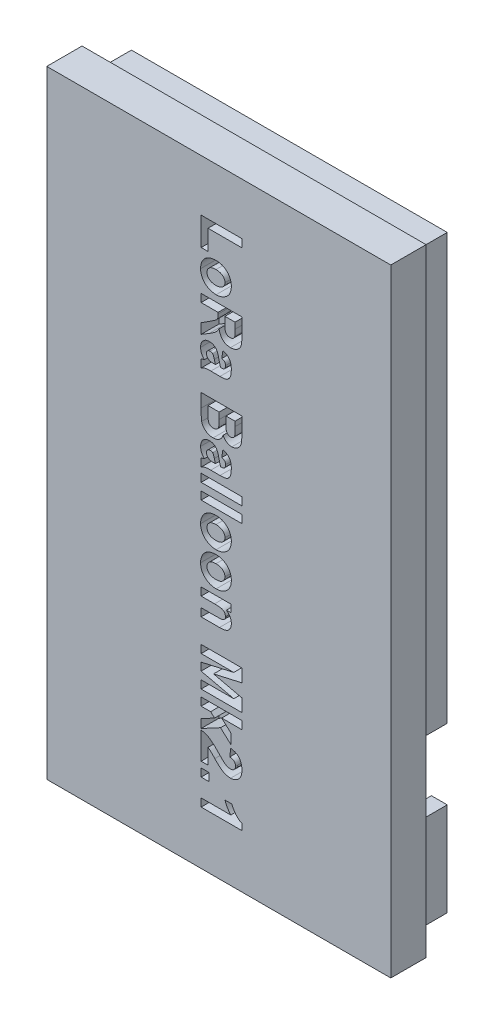
SolidWorks part; units mm, degrees
ref_plane "Front Plane" through (0, 0, 0) normal (0, 0, 1) x (1, 0, 0)
ref_plane "Top Plane" through (0, 0, 0) normal (0, 1, 0) x (1, 0, 0)
ref_plane "Right Plane" through (0, 0, 0) normal (1, 0, 0) x (0, 0, -1)
sketch "Sketch1" plane through (0, 0, 0) normal (0, 0, 1) x (1, 0, 0)
  line L1 (0, 0) -> (39, 0)
  line L2 (0, 0) -> (0, 70)
  line L3 (0, 70) -> (39, 70)
  line L4 (39, 0) -> (39, 70)
  dimension "D1" = 70
  dimension "D2" = 39
extrude "Base" add sketch "Sketch1" along normal blind 4
sketch "Sketch2" plane through (0, 0, 0) normal (0, 0, -1) x (-1, 0, 0)
  line L0 (-39, 0) -> (-39, 70) construction
  line L1 (-37.4, 68.4) -> (-35.6, 68.4)
  line L2 (-37.4, 68.4) -> (-37.4, 1.6)
  line L3 (-37.4, 1.6) -> (-35.6, 1.6)
  line L4 (-35.6, 68.4) -> (-35.6, 1.6)
  line L5 (0, 0) -> (-39, 0) construction
  line L6 (0, 70) -> (0, 0) construction
  line L7 (-35.6, 1.6) -> (-1.6, 1.6)
  line L8 (-35.6, 1.6) -> (-35.6, 3.4)
  line L9 (-35.6, 3.4) -> (-1.6, 3.4)
  line L10 (-1.6, 1.6) -> (-1.6, 3.4)
  line L12 (-39, 70) -> (0, 70) construction
  line L13 (-39, 35) -> (0, 35) construction
  line L14 (-19.5, 70) -> (-19.5, 0) construction
  line L15 (-35.6, 66.6) -> (-1.6, 66.6)
  line L16 (-1.6, 68.4) -> (-1.6, 66.6)
  line L17 (-35.6, 68.4) -> (-1.6, 68.4)
  line L18 (-35.6, 68.4) -> (-35.6, 66.6)
  line L19 (-1.6, 1.6) -> (-3.4, 1.6)
  line L20 (-3.4, 68.4) -> (-3.4, 1.6)
  line L21 (-1.6, 68.4) -> (-3.4, 68.4)
  line L22 (-1.6, 68.4) -> (-1.6, 1.6)
  dimension "D1" = 1.6
  dimension "D2" = 1.8
  dimension "D3" = 1.6
  dimension "D4" = 1.8
extrude "Mount" add sketch "Sketch2" along normal blind 4 contours L4 L1 L2 L3 | L22 L15 L20 L9 | L20 L9 L4 L7 | L9 L20 L7 L10 | L17 L20 L15 L16 | L20 L17 L4 L15
sketch "Sketch3" plane through (0, 0, 4) normal (0, 0, 1) x (1, 0, 0)
  line L0 (17.5, 0) -> (17.5, 70) construction
  line L1 (19.5, 0) -> (19.5, 5) construction
  line L2 (19.5, 70) -> (19.5, 65) construction
  line L3 (39, 70) -> (0, 70) construction
  line L4 (0, 0) -> (39, 0) construction
  line L6 (0, 70) -> (0, 0) construction
  text T0 "<b>  LoRa Balloon Mk2.1</b>" font "Arial Narrow" height in points 18
  dimension "D1" = 17.5
  dimension "D2" = 70
  dimension "D3" = 5
  dimension "D4" = 5
extrude "Name" cut sketch "Sketch3" against normal blind 2
sketch "Sketch4" plane through (35.6, 0, 0) normal (-1, 0, 0) x (0, 0, 1)
  line L0 (-4, 66.6) -> (-4, 3.4) construction
  line L1 (-4, 12.2) -> (0, 12.2)
  line L2 (-4, 12.2) -> (-4, 20.2)
  line L3 (-4, 20.2) -> (0, 20.2)
  line L4 (0, 12.2) -> (0, 20.2)
  line L5 (0, 66.6) -> (0, 3.4) construction
  line L6 (-4, 3.4) -> (0, 3.4) construction
  dimension "D1" = 8.8
  dimension "D2" = 8
extrude "Cut-Extrude1" cut sketch "Sketch4" against normal blind 1.8
sketch "Sketch5" plane through (0, 1.6, 0) normal (0, -1, 0) x (1, 0, 0)
  line L0 (37.4, -4) -> (1.6, -4) construction
  line L1 (9.1, -4) -> (19.1, -4)
  line L2 (9.1, -4) -> (9.1, 0)
  line L3 (9.1, 0) -> (19.1, 0)
  line L4 (19.1, -4) -> (19.1, 0)
  line L5 (37.4, 0) -> (1.6, 0) construction
  line L6 (1.6, -4) -> (1.6, 0) construction
  dimension "D1" = 7.5
  dimension "D2" = 17.5
extrude "Cut-Extrude2" cut sketch "Sketch5" against normal blind 1.8
